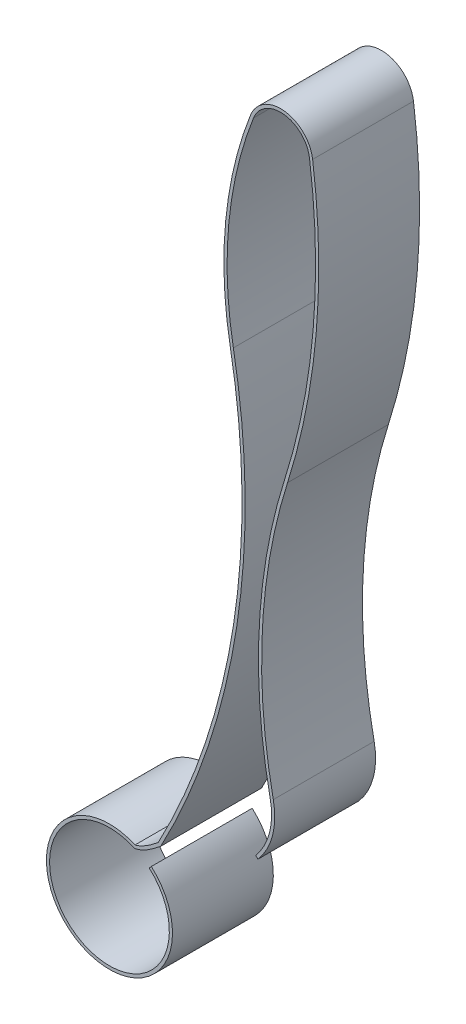
SolidWorks part; units mm, degrees
material "1060 Alloy"
ref_plane "Front Plane" through (0, 0, 0) normal (0, 0, 1) x (1, 0, 0)
ref_plane "Top Plane" through (0, 0, 0) normal (0, 1, 0) x (1, 0, 0)
ref_plane "Right Plane" through (0, 0, 0) normal (1, 0, 0) x (0, 0, -1)
sketch "Sketch1" plane through (0, 0, 0) normal (0, 0, 1) x (1, 0, 0)
  line L0 (-8.282, 14.5722) -> (-8.3153, 14.5349)
  line L1 (-6.6279, 15.5516) -> (-6.59, 15.519)
  arc A0 (-8.5818, 14.7561) -> (-8.282, 14.5722) centre (-8.9465, 13.8249) ccw construction
  arc A1 (-8.5408, 14.7389) -> (-8.282, 14.5722) centre (-8.9465, 13.8249) ccw
  arc A2 (-8.1727, 14.9561) -> (-7.0299, 22.3389) centre (-18.2024, 20.2885) ccw
  arc A3 (-7.0299, 22.3389) -> (-6.7078, 25.6845) centre (-0.9958, 23.4462) cw
  arc A4 (-6.7078, 25.6845) -> (-5.7229, 25.5664) centre (-6.2307, 25.4976) cw
  arc A5 (-5.7229, 25.5664) -> (-6.1215, 20.9246) centre (-16.2816, 24.1352) cw
  arc A6 (-6.1215, 20.9246) -> (-6.347, 16.4586) centre (2.3095, 18.2603) ccw
  arc A7 (-6.347, 16.4586) -> (-6.59, 15.519) centre (-7.421, 16.2351) cw
  arc A8 (-8.546, 14.6864) -> (-8.3153, 14.5349) centre (-8.9465, 13.8249) ccw
  arc A9 (-8.1332, 14.924) -> (-6.9807, 22.3479) centre (-18.2024, 20.2885) ccw
  arc A10 (-6.9807, 22.3479) -> (-6.6612, 25.6663) centre (-0.9958, 23.4462) cw
  arc A11 (-6.6612, 25.6663) -> (-5.7724, 25.5597) centre (-6.2307, 25.4976) cw
  arc A12 (-5.7724, 25.5597) -> (-6.1692, 20.9396) centre (-16.2816, 24.1352) cw
  arc A13 (-6.1692, 20.9396) -> (-6.3959, 16.4484) centre (2.3095, 18.2603) ccw
  arc A14 (-6.3959, 16.4484) -> (-6.6279, 15.5516) centre (-7.421, 16.2351) cw
  arc A15 (-8.1727, 14.9561) -> (-7.0299, 22.3389) centre (-18.2024, 20.2885) ccw construction
  spline S0 degree 2 poles (-8.5408, 14.7389) (-8.3919, 14.7737) (-8.1727, 14.9561) knots 0 0 0 1 1 1
  spline S1 degree 1 poles (-8.546, 14.6864) (-8.1332, 14.924) knots 0 0 1 1 construction
  spline S2 degree 3 poles (-8.546, 14.6864) (-8.4795, 14.7019) (-8.371, 14.7428) (-8.2037, 14.8653) (-8.1332, 14.924) knots -0.055624 -0.055624 -0.055624 -0.055624 0.480785 1.017194 1.017194 1.017194 1.017194
  dimension "D1" = 11.3591
  dimension "D2" = 6.1348
  dimension "D3" = 0.5124
  dimension "D4" = 10.6553
  dimension "D5" = 8.8419
  dimension "D6" = 1.097
  dimension "D7" = 0.95
  dimension "D8" = 2.3095
  dimension "D9" = 0.9958
  dimension "D10" = 5.7229
  dimension "D11" = 5.7724
  dimension "D12" = 6.347
  dimension "D13" = 6.9807
  dimension "D14" = 15.519
extrude "Boss-Extrude1" add sketch "Sketch1" along normal blind 1.6
